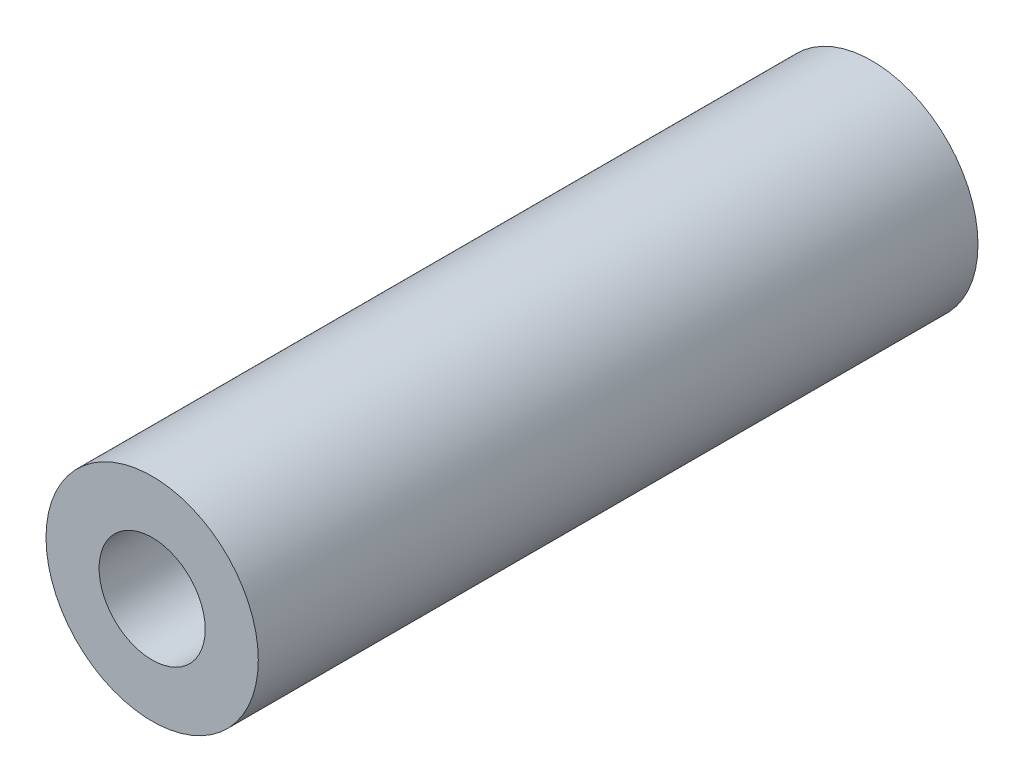
SolidWorks part; units mm, degrees
ref_plane "Front Plane" through (0, 0, 0) normal (0, 0, 1) x (1, 0, 0)
ref_plane "Top Plane" through (0, 0, 0) normal (0, 1, 0) x (1, 0, 0)
ref_plane "Right Plane" through (0, 0, 0) normal (1, 0, 0) x (0, 0, -1)
sketch "Sketch1" plane through (0, 0, 0) normal (0, 0, 1) x (1, 0, 0)
  circle A0 centre (0, 0) radius 5
  dimension "D1" = 10
extrude "Boss-Extrude1" add sketch "Sketch1" along normal blind 33.9
hole_wizard "Ø5.0mm Dowel Hole1" positions "Sketch2" profile "Sketch3" hole size "Ø5.0" standard "ANSI Metric" end condition up to next
sketch "Sketch2" plane through (0, 0, 33.9) normal (0, 0, 1) x (1, 0, 0)
  point P0 (0, 0)
sketch "Sketch3" plane through (0, 0, 33.9) normal (1, 0, 0) x (0, -1, 0)
  line L0 (0, 0) -> (0, 33.9)
  line L1 (0, 33.9) -> (2.5, 33.9)
  line L2 (2.5, 33.9) -> (2.5, 0)
  line L5 (2.5, 0) -> (0, 0)
  line L11 (0, -6.35) -> (0, 107.95) construction
  dimension "Thru Hole Dia." = 5
  dimension "Thru Hole Depth" = 33.9
